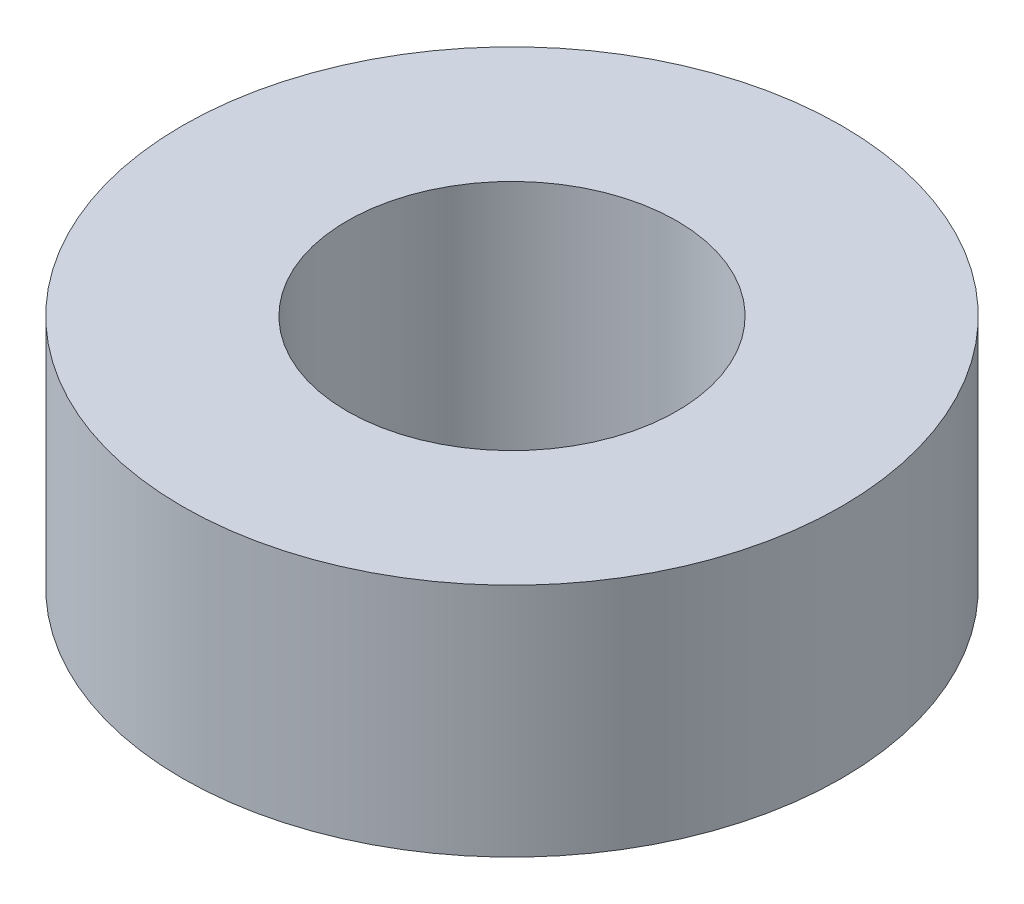
SolidWorks part; units mm, degrees
ref_plane "Front Plane" through (0, 0, 0) normal (0, 0, 1) x (1, 0, 0)
ref_plane "Top Plane" through (0, 0, 0) normal (0, 1, 0) x (1, 0, 0)
ref_plane "Right Plane" through (0, 0, 0) normal (1, 0, 0) x (0, 0, -1)
sketch "Sketch1" plane through (0, 0, 0) normal (0, 1, 0) x (1, 0, 0)
  circle A0 centre (0, 0) radius 7
  circle A1 centre (0, 0) radius 3.5
  dimension "D1" = 14
  dimension "D2" = 7
extrude "Boss-Extrude1" add sketch "Sketch1" along normal blind 5
